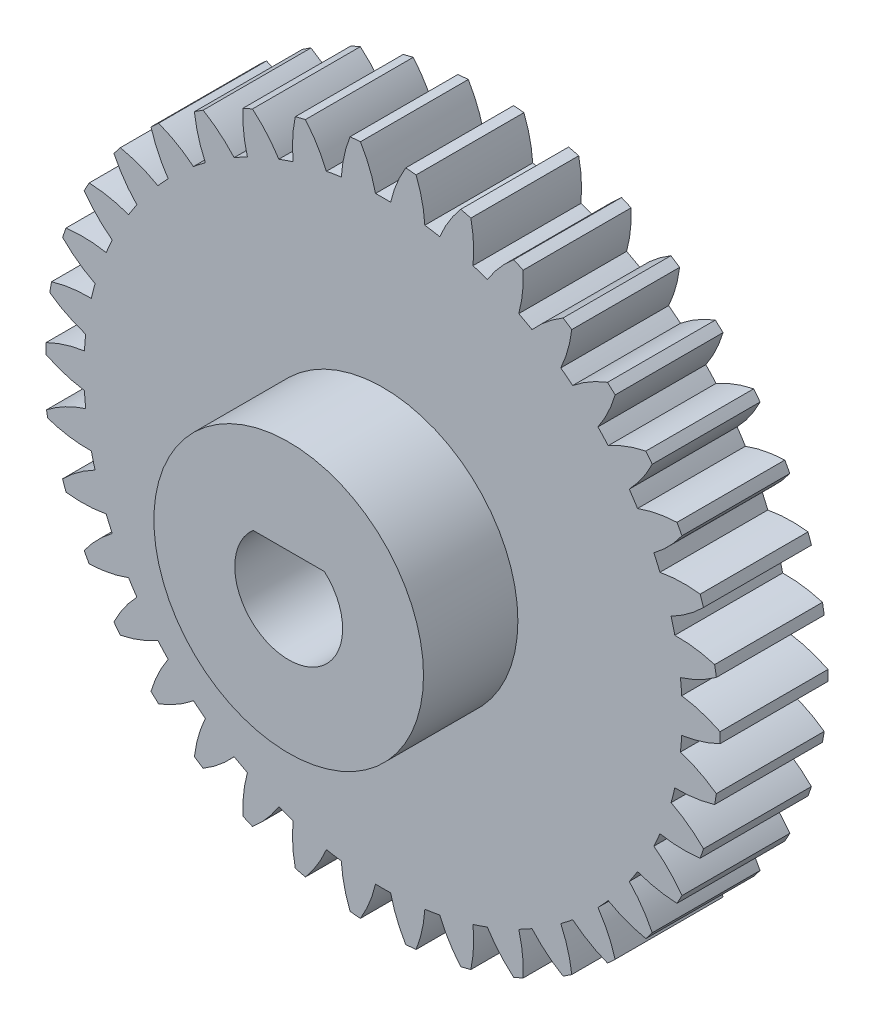
SolidWorks part; units mm, degrees
ref_plane "Front Plane" through (0, 0, 0) normal (0, 0, 1) x (1, 0, 0)
ref_plane "Top Plane" through (0, 0, 0) normal (0, 1, 0) x (1, 0, 0)
ref_plane "Right Plane" through (0, 0, 0) normal (1, 0, 0) x (0, 0, -1)
sketch "Sketch2" plane through (0, 0, 0) normal (0, 0, 1) x (1, 0, 0)
  line L0 (2.6458, 3) -> (-2.6458, 3)
  arc A0 (-2.6458, 3) -> (2.6458, 3) centre (0, 0) ccw
  arc A1 (-24.997, -0.3868) -> (-22.1499, -1.2731) centre (-20.7849, 8.1283) ccw
  arc A2 (-22.1499, -1.2731) -> (-22.0574, -2.39) centre (0, 0) ccw
  arc A3 (-22.0574, -2.39) -> (-24.9611, -3.9127) centre (-19.1635, -11.4385) ccw
  arc A4 (-24.9611, -3.9127) -> (-24.8791, -4.4041) centre (0, 0) ccw
  arc A5 (-24.8791, -4.4041) -> (-21.6383, -4.9015) centre (-21.8393, 4.5964) ccw
  arc A6 (-21.6383, -4.9015) -> (-21.3632, -5.988) centre (0, 0) ccw
  arc A7 (-21.3632, -5.988) -> (-23.7682, -7.7506) centre (-17.0194, -14.4367) ccw
  arc A8 (-23.7682, -7.7506) -> (-23.517, -8.4824) centre (0, 0) ccw
  arc A9 (-23.517, -8.4824) -> (-20.5364, -8.3962) centre (-22.2979, 0.9391) ccw
  arc A10 (-20.5364, -8.3962) -> (-20.0862, -9.4225) centre (0, 0) ccw
  arc A11 (-20.0862, -9.4225) -> (-22.1683, -11.557) centre (-14.4111, -17.0411) ccw
  arc A12 (-22.1683, -11.557) -> (-21.8001, -12.2375) centre (0, 0) ccw
  arc A13 (-21.8001, -12.2375) -> (-18.8744, -11.6619) centre (-22.1484, -2.7439) ccw
  arc A14 (-18.8744, -11.6619) -> (-18.2614, -12.6001) centre (0, 0) ccw
  arc A15 (-18.2614, -12.6001) -> (-19.9638, -15.0482) centre (-11.4097, -19.1807) ccw
  arc A16 (-19.9638, -15.0482) -> (-19.4885, -15.6588) centre (0, 0) ccw
  arc A17 (-19.4885, -15.6588) -> (-16.6975, -14.6094) centre (-21.3947, -6.3519) ccw
  arc A18 (-16.6975, -14.6094) -> (-15.9384, -15.434) centre (0, 0) ccw
  arc A19 (-15.9384, -15.434) -> (-17.2146, -18.1289) centre (-8.097, -20.7971) ccw
  arc A20 (-17.2146, -18.1289) -> (-16.6454, -18.6529) centre (0, 0) ccw
  arc A21 (-16.6454, -18.6529) -> (-14.0651, -17.1585) centre (-20.0574, -9.7868) ccw
  arc A22 (-14.0651, -17.1585) -> (-13.1807, -17.8469) centre (0, 0) ccw
  arc A23 (-13.1807, -17.8469) -> (-13.9959, -20.7151) centre (-4.5635, -21.8461) ccw
  arc A24 (-13.9959, -20.7151) -> (-13.3482, -21.1382) centre (0, 0) ccw
  arc A25 (-13.3482, -21.1382) -> (-11.0491, -19.2395) centre (-18.173, -12.9546) ccw
  arc A26 (-11.0491, -19.2395) -> (-10.0634, -19.7729) centre (0, 0) ccw
  arc A27 (-10.0634, -19.7729) -> (-10.3954, -22.7362) centre (-0.9055, -22.2993) ccw
  arc A28 (-10.3954, -22.7362) -> (-9.6869, -23.047) centre (0, 0) ccw
  arc A29 (-9.6869, -23.047) -> (-7.7317, -20.7957) centre (-15.7929, -15.7691) ccw
  arc A30 (-7.7317, -20.7957) -> (-6.6716, -21.1596) centre (0, 0) ccw
  arc A31 (-6.6716, -21.1596) -> (-6.5114, -24.1371) centre (2.7772, -22.1442) ccw
  arc A32 (-6.5114, -24.1371) -> (-5.7614, -24.3271) centre (0, 0) ccw
  arc A33 (-5.7614, -24.3271) -> (-4.2033, -21.7847) centre (-12.982, -18.1535) ccw
  arc A34 (-4.2033, -21.7847) -> (-3.0979, -21.9692) centre (0, 0) ccw
  arc A35 (-3.0979, -21.9692) -> (-2.4498, -24.8797) centre (6.3841, -21.3851) ccw
  arc A36 (-2.4498, -24.8797) -> (-1.6787, -24.9436) centre (0, 0) ccw
  arc A37 (-1.6787, -24.9436) -> (-0.5604, -22.1794) centre (-9.8169, -20.0426) ccw
  arc A38 (-0.5604, -22.1794) -> (0.5604, -22.1794) centre (0, 0) ccw
  arc A39 (0.5604, -22.1794) -> (1.6787, -24.9436) centre (9.8169, -20.0426) ccw
  arc A40 (1.6787, -24.9436) -> (2.4498, -24.8797) centre (0, 0) ccw
  arc A41 (2.4498, -24.8797) -> (3.0979, -21.9692) centre (-6.3841, -21.3851) ccw
  arc A42 (3.0979, -21.9692) -> (4.2033, -21.7847) centre (0, 0) ccw
  arc A43 (4.2033, -21.7847) -> (5.7614, -24.3271) centre (12.982, -18.1535) ccw
  arc A44 (5.7614, -24.3271) -> (6.5114, -24.1371) centre (0, 0) ccw
  arc A45 (6.5114, -24.1371) -> (6.6716, -21.1596) centre (-2.7772, -22.1442) ccw
  arc A46 (6.6716, -21.1596) -> (7.7317, -20.7957) centre (0, 0) ccw
  arc A47 (7.7317, -20.7957) -> (9.6869, -23.047) centre (15.7929, -15.7691) ccw
  arc A48 (9.6869, -23.047) -> (10.3954, -22.7362) centre (0, 0) ccw
  arc A49 (10.3954, -22.7362) -> (10.0634, -19.7729) centre (0.9055, -22.2993) ccw
  arc A50 (10.0634, -19.7729) -> (11.0491, -19.2395) centre (0, 0) ccw
  arc A51 (11.0491, -19.2395) -> (13.3482, -21.1382) centre (18.173, -12.9546) ccw
  arc A52 (13.3482, -21.1382) -> (13.9959, -20.7151) centre (0, 0) ccw
  arc A53 (13.9959, -20.7151) -> (13.1807, -17.8469) centre (4.5635, -21.8461) ccw
  arc A54 (13.1807, -17.8469) -> (14.0651, -17.1585) centre (0, 0) ccw
  arc A55 (14.0651, -17.1585) -> (16.6454, -18.6529) centre (20.0574, -9.7868) ccw
  arc A56 (16.6454, -18.6529) -> (17.2146, -18.1289) centre (0, 0) ccw
  arc A57 (17.2146, -18.1289) -> (15.9384, -15.434) centre (8.097, -20.7971) ccw
  arc A58 (15.9384, -15.434) -> (16.6975, -14.6094) centre (0, 0) ccw
  arc A59 (16.6975, -14.6094) -> (19.4885, -15.6588) centre (21.3947, -6.3519) ccw
  arc A60 (19.4885, -15.6588) -> (19.9638, -15.0482) centre (0, 0) ccw
  arc A61 (19.9638, -15.0482) -> (18.2614, -12.6001) centre (11.4097, -19.1807) ccw
  arc A62 (18.2614, -12.6001) -> (18.8744, -11.6619) centre (0, 0) ccw
  arc A63 (18.8744, -11.6619) -> (21.8001, -12.2375) centre (22.1484, -2.7439) ccw
  arc A64 (21.8001, -12.2375) -> (22.1683, -11.557) centre (0, 0) ccw
  arc A65 (22.1683, -11.557) -> (20.0862, -9.4225) centre (14.4111, -17.0411) ccw
  arc A66 (20.0862, -9.4225) -> (20.5364, -8.3962) centre (0, 0) ccw
  arc A67 (20.5364, -8.3962) -> (23.517, -8.4824) centre (22.2979, 0.9391) ccw
  arc A68 (23.517, -8.4824) -> (23.7682, -7.7506) centre (0, 0) ccw
  arc A69 (23.7682, -7.7506) -> (21.3632, -5.988) centre (17.0194, -14.4367) ccw
  arc A70 (21.3632, -5.988) -> (21.6383, -4.9015) centre (0, 0) ccw
  arc A71 (21.6383, -4.9015) -> (24.5924, -4.4959) centre (21.8393, 4.5964) ccw
  arc A72 (24.5924, -4.4959) -> (24.7198, -3.7328) centre (0, 0) ccw
  arc A73 (24.7198, -3.7328) -> (22.0574, -2.39) centre (19.1635, -11.4385) ccw
  arc A74 (22.0574, -2.39) -> (22.1499, -1.2731) centre (0, 0) ccw
  arc A75 (22.1499, -1.2731) -> (24.997, -0.3868) centre (20.7849, 8.1283) ccw
  arc A76 (24.997, -0.3868) -> (24.997, 0.3868) centre (0, 0) ccw
  arc A77 (24.997, 0.3868) -> (22.1499, 1.2731) centre (20.7849, -8.1283) ccw
  arc A78 (22.1499, 1.2731) -> (22.0574, 2.39) centre (0, 0) ccw
  arc A79 (22.0574, 2.39) -> (24.7198, 3.7328) centre (19.1635, 11.4385) ccw
  arc A80 (24.7198, 3.7328) -> (24.5924, 4.4959) centre (0, 0) ccw
  arc A81 (24.5924, 4.4959) -> (21.6383, 4.9015) centre (21.8393, -4.5964) ccw
  arc A82 (21.6383, 4.9015) -> (21.3632, 5.988) centre (0, 0) ccw
  arc A83 (21.3632, 5.988) -> (23.7682, 7.7506) centre (17.0194, 14.4367) ccw
  arc A84 (23.7682, 7.7506) -> (23.517, 8.4824) centre (0, 0) ccw
  arc A85 (23.517, 8.4824) -> (20.5364, 8.3962) centre (22.2979, -0.9391) ccw
  arc A86 (20.5364, 8.3962) -> (20.0862, 9.4225) centre (0, 0) ccw
  arc A87 (20.0862, 9.4225) -> (22.1683, 11.557) centre (14.4111, 17.0411) ccw
  arc A88 (22.1683, 11.557) -> (21.8001, 12.2375) centre (0, 0) ccw
  arc A89 (21.8001, 12.2375) -> (18.8744, 11.6619) centre (22.1484, 2.7439) ccw
  arc A90 (18.8744, 11.6619) -> (18.2614, 12.6001) centre (0, 0) ccw
  arc A91 (18.2614, 12.6001) -> (19.9638, 15.0482) centre (11.4097, 19.1807) ccw
  arc A92 (19.9638, 15.0482) -> (19.4885, 15.6588) centre (0, 0) ccw
  arc A93 (19.4885, 15.6588) -> (16.6975, 14.6094) centre (21.3947, 6.3519) ccw
  arc A94 (16.6975, 14.6094) -> (15.9384, 15.434) centre (0, 0) ccw
  arc A95 (15.9384, 15.434) -> (17.2146, 18.1289) centre (8.097, 20.7971) ccw
  arc A96 (17.2146, 18.1289) -> (16.6454, 18.6529) centre (0, 0) ccw
  arc A97 (16.6454, 18.6529) -> (14.0651, 17.1585) centre (20.0574, 9.7868) ccw
  arc A98 (14.0651, 17.1585) -> (13.1807, 17.8469) centre (0, 0) ccw
  arc A99 (13.1807, 17.8469) -> (13.9959, 20.7151) centre (4.5635, 21.8461) ccw
  arc A100 (13.9959, 20.7151) -> (13.3482, 21.1382) centre (0, 0) ccw
  arc A101 (13.3482, 21.1382) -> (11.0491, 19.2395) centre (18.173, 12.9546) ccw
  arc A102 (11.0491, 19.2395) -> (10.0634, 19.7729) centre (0, 0) ccw
  arc A103 (10.0634, 19.7729) -> (10.3954, 22.7362) centre (0.9055, 22.2993) ccw
  arc A104 (10.3954, 22.7362) -> (9.6869, 23.047) centre (0, 0) ccw
  arc A105 (9.6869, 23.047) -> (7.7317, 20.7957) centre (15.7929, 15.7691) ccw
  arc A106 (7.7317, 20.7957) -> (6.6716, 21.1596) centre (0, 0) ccw
  arc A107 (6.6716, 21.1596) -> (6.5114, 24.1371) centre (-2.7772, 22.1442) ccw
  arc A108 (6.5114, 24.1371) -> (5.7614, 24.3271) centre (0, 0) ccw
  arc A109 (5.7614, 24.3271) -> (4.2033, 21.7847) centre (12.982, 18.1535) ccw
  arc A110 (4.2033, 21.7847) -> (3.0979, 21.9692) centre (0, 0) ccw
  arc A111 (3.0979, 21.9692) -> (2.4498, 24.8797) centre (-6.3841, 21.3851) ccw
  arc A112 (2.4498, 24.8797) -> (1.6787, 24.9436) centre (0, 0) ccw
  arc A113 (1.6787, 24.9436) -> (0.5604, 22.1794) centre (9.8169, 20.0426) ccw
  arc A114 (0.5604, 22.1794) -> (-0.5604, 22.1794) centre (0, 0) ccw
  arc A115 (-0.5604, 22.1794) -> (-1.6787, 24.9436) centre (-9.8169, 20.0426) ccw
  arc A116 (-1.6787, 24.9436) -> (-2.4498, 24.8797) centre (0, 0) ccw
  arc A117 (-2.4498, 24.8797) -> (-3.0979, 21.9692) centre (6.3841, 21.3851) ccw
  arc A118 (-3.0979, 21.9692) -> (-4.2033, 21.7847) centre (0, 0) ccw
  arc A119 (-4.2033, 21.7847) -> (-5.7614, 24.3271) centre (-12.982, 18.1535) ccw
  arc A120 (-5.7614, 24.3271) -> (-6.5114, 24.1371) centre (0, 0) ccw
  arc A121 (-6.5114, 24.1371) -> (-6.6716, 21.1596) centre (2.7772, 22.1442) ccw
  arc A122 (-6.6716, 21.1596) -> (-7.7317, 20.7957) centre (0, 0) ccw
  arc A123 (-7.7317, 20.7957) -> (-9.6869, 23.047) centre (-15.7929, 15.7691) ccw
  arc A124 (-9.6869, 23.047) -> (-10.3954, 22.7362) centre (0, 0) ccw
  arc A125 (-10.3954, 22.7362) -> (-10.0634, 19.7729) centre (-0.9055, 22.2993) ccw
  arc A126 (-10.0634, 19.7729) -> (-11.0491, 19.2395) centre (0, 0) ccw
  arc A127 (-11.0491, 19.2395) -> (-13.3482, 21.1382) centre (-18.173, 12.9546) ccw
  arc A128 (-13.3482, 21.1382) -> (-13.9959, 20.7151) centre (0, 0) ccw
  arc A129 (-13.9959, 20.7151) -> (-13.1807, 17.8469) centre (-4.5635, 21.8461) ccw
  arc A130 (-13.1807, 17.8469) -> (-14.0651, 17.1585) centre (0, 0) ccw
  arc A131 (-14.0651, 17.1585) -> (-16.6454, 18.6529) centre (-20.0574, 9.7868) ccw
  arc A132 (-16.6454, 18.6529) -> (-17.2146, 18.1289) centre (0, 0) ccw
  arc A133 (-17.2146, 18.1289) -> (-15.9384, 15.434) centre (-8.097, 20.7971) ccw
  arc A134 (-15.9384, 15.434) -> (-16.6975, 14.6094) centre (0, 0) ccw
  arc A135 (-16.6975, 14.6094) -> (-19.4885, 15.6588) centre (-21.3947, 6.3519) ccw
  arc A136 (-19.4885, 15.6588) -> (-19.9638, 15.0482) centre (0, 0) ccw
  arc A137 (-19.9638, 15.0482) -> (-18.2614, 12.6001) centre (-11.4097, 19.1807) ccw
  arc A138 (-18.2614, 12.6001) -> (-18.8744, 11.6619) centre (0, 0) ccw
  arc A139 (-18.8744, 11.6619) -> (-21.8001, 12.2375) centre (-22.1484, 2.7439) ccw
  arc A140 (-21.8001, 12.2375) -> (-22.1683, 11.557) centre (0, 0) ccw
  arc A141 (-22.1683, 11.557) -> (-20.0862, 9.4225) centre (-14.4111, 17.0411) ccw
  arc A142 (-20.0862, 9.4225) -> (-20.5364, 8.3962) centre (0, 0) ccw
  arc A143 (-20.5364, 8.3962) -> (-23.517, 8.4824) centre (-22.2979, -0.9391) ccw
  arc A144 (-23.517, 8.4824) -> (-23.7682, 7.7506) centre (0, 0) ccw
  arc A145 (-23.7682, 7.7506) -> (-21.3632, 5.988) centre (-17.0194, 14.4367) ccw
  arc A146 (-21.3632, 5.988) -> (-21.6383, 4.9015) centre (0, 0) ccw
  arc A147 (-21.6383, 4.9015) -> (-24.5924, 4.4959) centre (-21.8393, -4.5964) ccw
  arc A148 (-24.5924, 4.4959) -> (-24.7198, 3.7328) centre (0, 0) ccw
  arc A149 (-24.7198, 3.7328) -> (-22.0574, 2.39) centre (-19.1635, 11.4385) ccw
  arc A150 (-22.0574, 2.39) -> (-22.1499, 1.2731) centre (0, 0) ccw
  arc A151 (-22.1499, 1.2731) -> (-24.997, 0.3868) centre (-20.7849, -8.1283) ccw
  arc A152 (-24.997, 0.3868) -> (-24.997, -0.3868) centre (0, 0) ccw
  dimension "D1" = 4
  dimension "D2" = 3
extrude "Boss-Extrude1" add sketch "Sketch2" along normal blind 8
sketch "Sketch3" plane through (0, 0, 8) normal (0, 0, 1) x (1, 0, 0)
  line L0 (2.6458, 3) -> (-2.6458, 3) construction
  line L1 (2.6458, 3) -> (-2.6458, 3)
  circle A0 centre (0, 0) radius 10
  arc A1 (-2.6458, 3) -> (2.6458, 3) centre (0, 0) ccw construction
  arc A2 (-2.6458, 3) -> (2.6458, 3) centre (0, 0) ccw
  dimension "D1" = 20
extrude "Boss-Extrude2" add sketch "Sketch3" along normal blind 7
